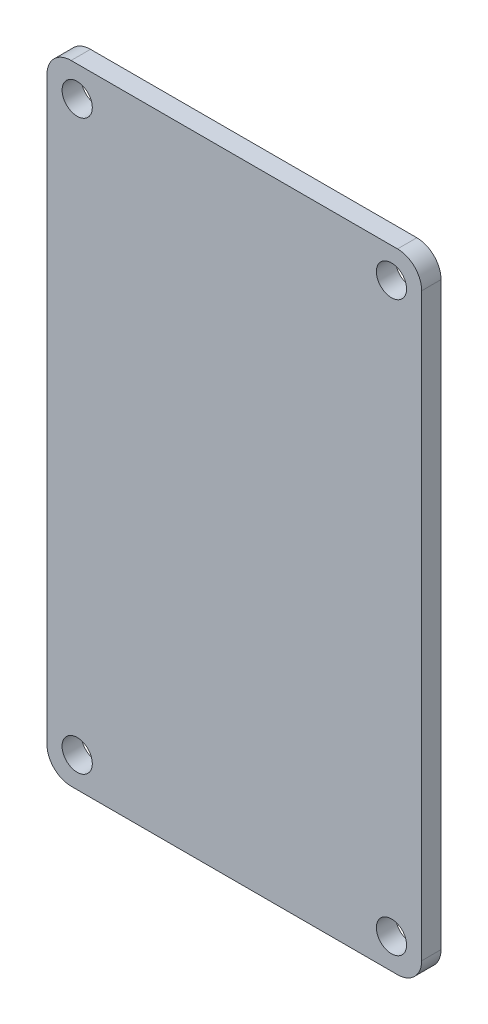
SolidWorks part; units mm, degrees
ref_plane "Спереди" through (0, 0, 0) normal (0, 0, 1) x (1, 0, 0)
ref_plane "Сверху" through (0, 0, 0) normal (0, 1, 0) x (1, 0, 0)
ref_plane "Справа" through (0, 0, 0) normal (1, 0, 0) x (0, 0, -1)
sketch "Sketch1" plane through (0, 0, 0) normal (0, 0, 1) x (1, 0, 0)
  line L0 (0, 26) -> (0, -26) construction
  line L1 (-13.5, 26) -> (13.5, 26)
  line L2 (-15.5, 24) -> (-15.5, -24)
  line L3 (-13.5, -26) -> (13.5, -26)
  line L4 (15.5, 24) -> (15.5, -24)
  line L5 (-15.5, 0) -> (15.5, 0) construction
  circle A0 centre (-13, 23.5) radius 1.25
  circle A1 centre (13, 23.5) radius 1.25
  circle A2 centre (13, -23.5) radius 1.25
  circle A3 centre (-13, -23.5) radius 1.25
  arc A4 (13.5, -26) -> (15.5, -24) centre (13.5, -24) ccw
  arc A5 (-15.5, -24) -> (-13.5, -26) centre (-13.5, -24) ccw
  arc A6 (13.5, 26) -> (15.5, 24) centre (13.5, 24) cw
  arc A7 (-13.5, 26) -> (-15.5, 24) centre (-13.5, 24) ccw
  dimension "D3" = 2.5
  dimension "D6" = 2
  dimension "D1" = 31
  dimension "D2" = 52
  dimension "D4" = 2.5
  dimension "D5" = 2.5
extrude "Boss-Extrude1" add sketch "Sketch1" along normal blind 1.6
